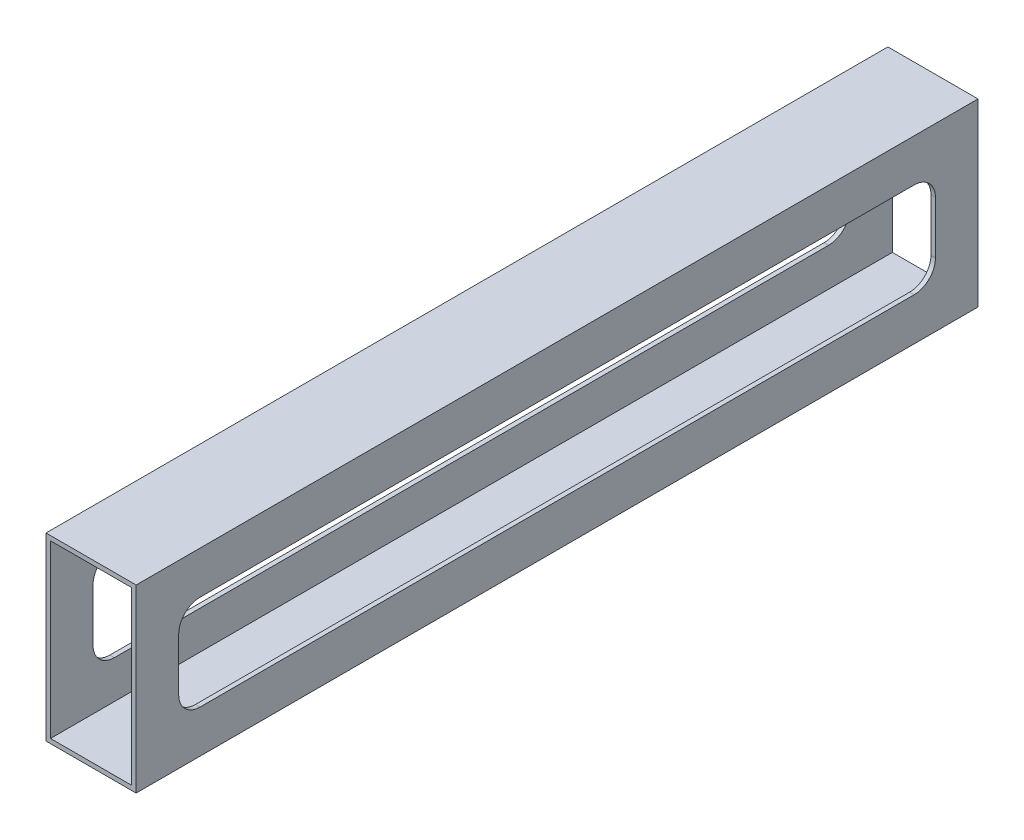
SolidWorks part; units mm, degrees
ref_plane "Front Plane" through (0, 0, 0) normal (0, 0, 1) x (1, 0, 0)
ref_plane "Top Plane" through (0, 0, 0) normal (0, 1, 0) x (1, 0, 0)
ref_plane "Right Plane" through (0, 0, 0) normal (1, 0, 0) x (0, 0, -1)
sketch "Sketch1" plane through (0, 0, 0) normal (0, 0, 1) x (1, 0, 0)
  line L0 (-107.6729, -9.7884) -> (-107.6729, -13.9706) construction
  line L1 (-97.6413, -9.7884) -> (-97.6413, -13.9706) construction
  line L2 (-107.6729, -11.8795) -> (-97.6413, -11.8795) construction
  line L3 (-114.0871, 12.2505) -> (-91.2271, 12.2505)
  line L4 (-115.3571, -37.2795) -> (-89.9571, -37.2795)
  line L5 (-115.3571, -37.2795) -> (-115.3571, 13.5205)
  line L6 (-115.3571, 13.5205) -> (-89.9571, 13.5205)
  line L7 (-89.9571, -37.2795) -> (-89.9571, 13.5205)
  line L8 (-91.2271, -36.0095) -> (-91.2271, 12.2505)
  line L9 (-114.0871, -36.0095) -> (-91.2271, -36.0095)
  line L10 (-42.1433, 13.5205) -> (-163.1708, 13.5205) construction
  line L11 (-114.0871, -36.0095) -> (-114.0871, 12.2505)
  point P10 (-102.6571, -11.8795)
  dimension "D1" = 50.8
  dimension "D2" = 25.4
  dimension "D3" = 1.27
extrude "Boss-Extrude1" add sketch "Sketch1" along normal up to surface (237.2995 mm away)
sketch "Sketch4" plane through (-89.9571, 0, 0) normal (1, 0, 0) x (0, 0, -1)
  line L10 (-12, 1.5205) -> (-225.2995, 1.5205)
  line L11 (-225.2995, 1.5205) -> (-225.2995, -25.2795)
  line L16 (-225.2995, -25.2795) -> (-12, -25.2795)
  line L17 (-12, -25.2795) -> (-12, 1.5205)
  line L18 (-18, 1.5205) -> (-219.2995, 1.5205)
  line L19 (-225.2995, -4.4795) -> (-225.2995, -19.2795)
  line L20 (-219.2995, -25.2795) -> (-18, -25.2795)
  line L21 (-12, -19.2795) -> (-12, -4.4795)
  arc A6 (-18, 1.5205) -> (-12, -4.4795) centre (-18, -4.4795) cw
  arc A7 (-18, -25.2795) -> (-12, -19.2795) centre (-18, -19.2795) ccw
  arc A8 (-225.2995, -19.2795) -> (-219.2995, -25.2795) centre (-219.2995, -19.2795) ccw
  arc A9 (-219.2995, 1.5205) -> (-225.2995, -4.4795) centre (-219.2995, -4.4795) ccw
  dimension "D2" = 6
  dimension "D1" = 12
extrude "Cut-Extrude5" cut sketch "Sketch4" against normal through all
